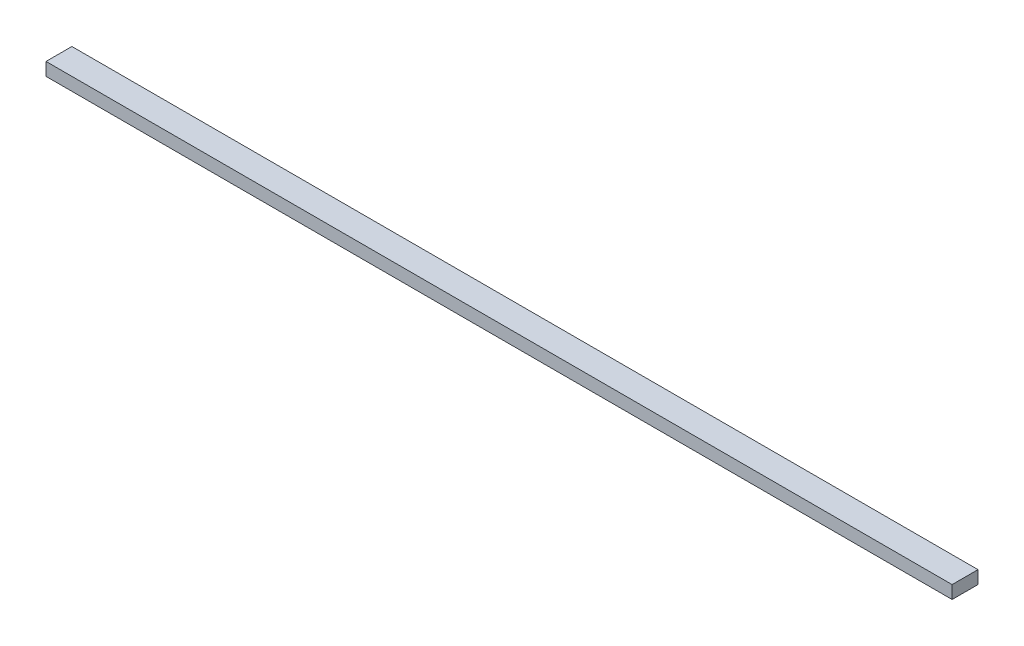
SolidWorks part; units mm, degrees
ref_plane "Face" through (0, 0, 0) normal (0, 0, 1) x (1, 0, 0)
ref_plane "Dessus" through (0, 0, 0) normal (0, 1, 0) x (1, 0, 0)
ref_plane "Droite" through (0, 0, 0) normal (1, 0, 0) x (0, 0, -1)
sketch "Esquisse1" plane through (0, 0, 0) normal (0, 1, 0) x (1, 0, 0)
  line L1 (0, 0) -> (700, 0)
  line L2 (0, 0) -> (0, 20)
  line L3 (0, 20) -> (700, 20)
  line L4 (700, 0) -> (700, 20)
  dimension "D1" = 20
  dimension "D2" = 700
extrude "Extrusion1" add sketch "Esquisse1" along normal blind 10
